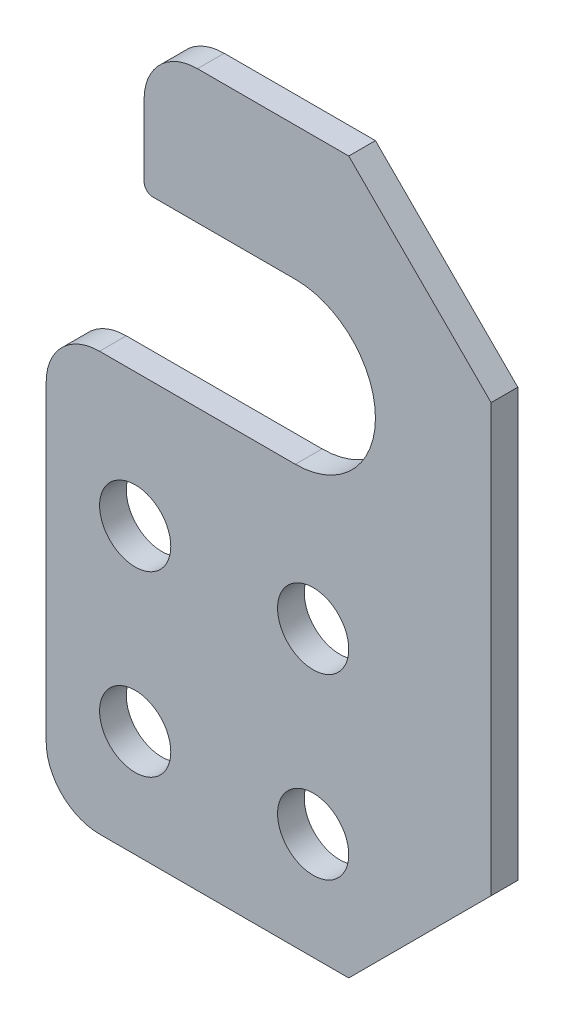
SolidWorks part; units mm, degrees
material "1060 Alloy"
ref_plane "Front Plane" through (0, 0, 0) normal (0, 0, 1) x (1, 0, 0)
ref_plane "Top Plane" through (0, 0, 0) normal (0, 1, 0) x (1, 0, 0)
ref_plane "Right Plane" through (0, 0, 0) normal (1, 0, 0) x (0, 0, -1)
sketch "Sketch1" plane through (0, 0, 0) normal (0, 0, 1) x (1, 0, 0)
  line L0 (20, -34) -> (10, -34) construction
  line L1 (0, 0) -> (30, 0)
  line L2 (0, 0) -> (0, -40)
  line L3 (0, -40) -> (30, -40)
  line L4 (30, 0) -> (30, -40)
  line L5 (10, -34) -> (15, -34) construction
  line L6 (15, -34) -> (15, -40) construction
  circle A0 centre (20, -34) radius 2
  circle A1 centre (10, -34) radius 2
  circle A2 centre (20, -24) radius 2
  circle A3 centre (10, -24) radius 2
  dimension "D1" = 4
  dimension "D2" = 4
  dimension "D3" = 6
  dimension "D4" = 10
  dimension "D5" = 40
  dimension "D6" = 30
  dimension "D7" = 10
extrude "Boss-Extrude1" add sketch "Sketch1" along normal blind 1.5
chamfer "Chamfer1" distance 8 angle 45 2 edges at (30, -40, 0.75) (30, 0, 0.75)
sketch "Sketch2" plane through (0, 0, 1.5) normal (0, 0, 1) x (1, 0, 0)
  line L0 (5, -16.5) -> (19, -16.5)
  line L1 (0, 0) -> (0, -40) construction
  line L2 (0, -7.5) -> (19, -7.5) construction
  line L3 (10.5, -12) -> (10.5, 0) construction
  line L4 (22, 0) -> (0, 0) construction
  line L5 (10.5, 0) -> (10.5, -7.5)
  line L6 (10.5, -7.5) -> (19, -7.5)
  line L7 (10.5, 0) -> (0, 0)
  line L8 (0, 0) -> (0, -16.5)
  line L9 (5, -16.5) -> (5, -40)
  line L10 (0, -40) -> (22, -40) construction
  line L11 (5, -40) -> (0, -40)
  line L12 (0, -40) -> (0, -16.5)
  circle A0 centre (6, -12) radius 4.5 construction
  circle A1 centre (15, -12) radius 4.5 construction
  circle A2 centre (8.5, -12) radius 4.5 construction
  arc A4 (19, -16.5) -> (19, -7.5) centre (19, -12) ccw
  dimension "D1" = 9
  dimension "D7" = 4
  dimension "D2" = 12
  dimension "D3" = 6
  dimension "D4" = 9
  dimension "D5" = 4.5
  dimension "D6" = 8.5
  dimension "D8" = 5
extrude "Cut-Extrude1" cut sketch "Sketch2" against normal blind 5
fillet "Fillet1" radius 3 3 edges at (10.5, 0, 0.75) (5, -40, 0.75) (5, -16.5, 0.75)
fillet "Fillet2" radius 0.5 1 edges at (10.5, -7.5, 0.75)
